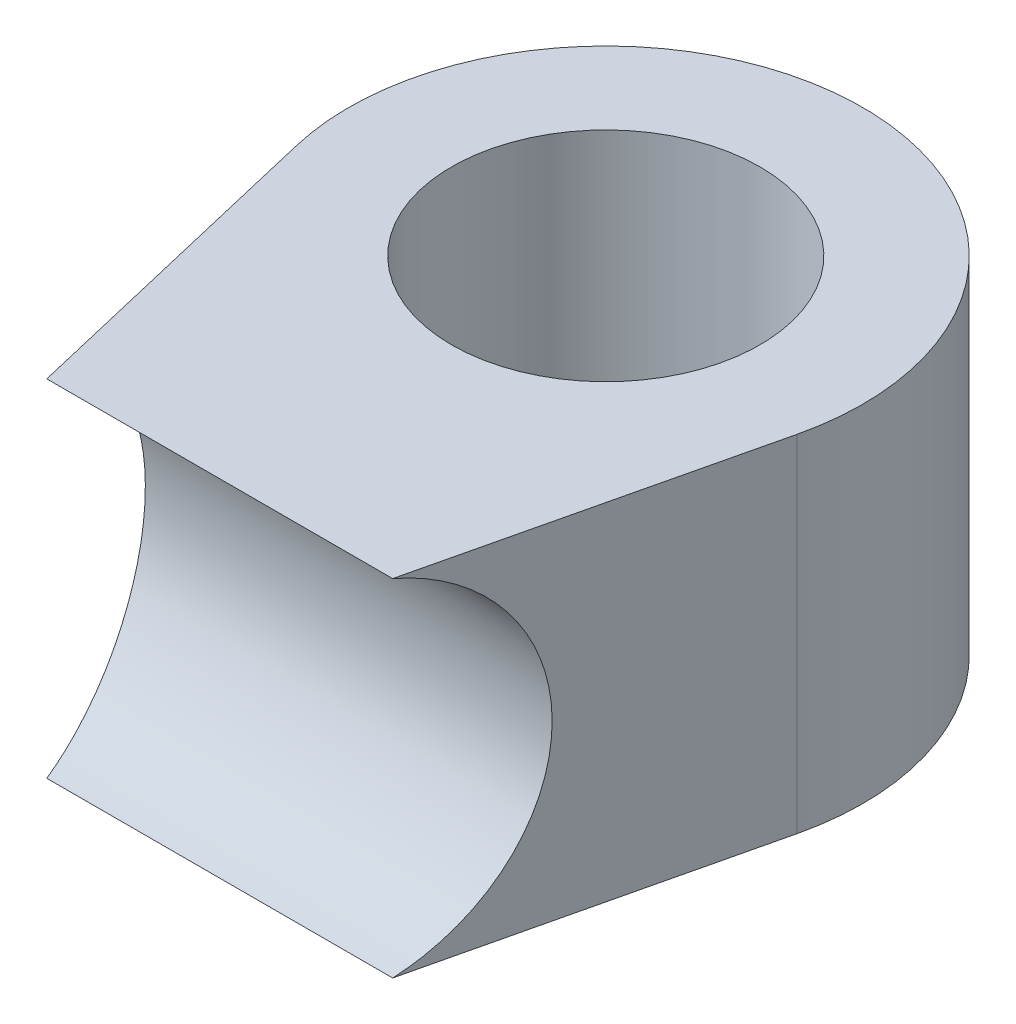
SolidWorks part; units mm, degrees
ref_plane "Front Plane" through (0, 0, 0) normal (0, 0, 1) x (1, 0, 0)
ref_plane "Top Plane" through (0, 0, 0) normal (0, 1, 0) x (1, 0, 0)
ref_plane "Right Plane" through (0, 0, 0) normal (1, 0, 0) x (0, 0, -1)
sketch "Croquis1" plane through (0, 0, 0) normal (0, 1, 0) x (1, 0, 0)
  line L0 (-3.3645, 1) -> (-4.8662, 7.3612)
  line L1 (3.3645, 1) -> (4.8662, 7.3612)
  line L2 (-10.0265, 1) -> (10.1268, 1)
  circle A0 centre (0, 0) radius 3.51
  circle A1 centre (0, 8.51) radius 5
  circle A2 centre (0, 8.51) radius 3
  dimension "D1" = 7.02
  dimension "11" = 10
  dimension "D4" = 6
  dimension "D3" = 1
extrude "Saliente-Extruir2" add sketch "Croquis1" along normal blind 10 contours A1 A0 L1 | A1 L0 A0 | A1 A2 | L2 A0
sketch "Croquis2" plane through (0, 0, 0) normal (1, 0, 0) x (0, 0, -1)
  line L2 (1, 10) -> (1, 0) construction
  circle A0 centre (0, 3.3645) radius 3.51
  dimension "D1" = 7.02
  dimension "D2" = 1
extrude "Cortar-Extruir1" cut sketch "Croquis2" against normal through all both and the other way through all
sketch "Croquis4" plane through (0, 0, -1) normal (0, 0, 1) x (1, 0, 0)
  line L0 (-10.382, 6.7291) -> (12.6514, 6.7291)
  line L1 (-3.3645, 6.7291) -> (3.3645, 6.7291) construction
  line L2 (-10.382, 6.7291) -> (-4.6185, 12.0955)
  line L3 (-4.6185, 12.0955) -> (6.885, 11.6851)
  line L4 (6.885, 11.6851) -> (12.6514, 6.7291)
extrude "Cortar-Extruir2" cut sketch "Croquis4" against normal through all
